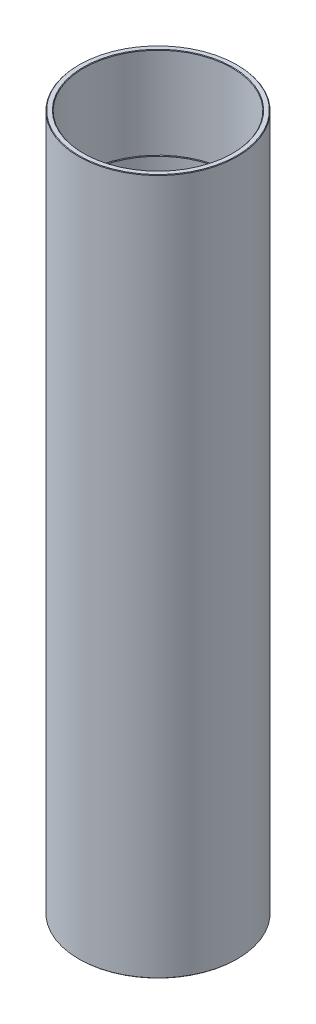
SolidWorks part; units mm, degrees
material "Технически чистый Сорт 2 продольный (SS)"
ref_plane "Спереди" through (0, 0, 0) normal (0, 0, 1) x (1, 0, 0)
ref_plane "Сверху" through (0, 0, 0) normal (0, 1, 0) x (1, 0, 0)
ref_plane "Справа" through (0, 0, 0) normal (1, 0, 0) x (0, 0, -1)
sketch "Эскиз1" plane through (0, 0, 0) normal (0, 0, 1) x (1, 0, 0)
  line L0 (0, 0) -> (0, 265) construction
  line L1 (-30.2, 0) -> (-30.2, 265)
  line L2 (-30.2, 265) -> (-28.25, 265)
  line L3 (-28.25, 265) -> (-28.25, 230)
  line L4 (-28.25, 230) -> (-28, 230)
  line L5 (-30.2, 0) -> (-28.25, 0)
  line L6 (-28.25, 0) -> (-28.25, 25)
  line L7 (-28.25, 25) -> (-28, 25)
  line L8 (-28, 25) -> (-28, 230)
  dimension "D1" = 30.2
  dimension "D2" = 28
  dimension "D3" = 28.25
  dimension "D4" = 28.25
  dimension "D5" = 25
  dimension "D6" = 35
revolve "Повернуть1" add sketch "Эскиз1" angle 360 about L0
chamfer "Фаска1" distance 0.2 angle 45 1 edges at (0, 265, -30.2)
chamfer "Фаска2" distance 0.2 angle 45 2 edges at (0, 230, -28.25) (0, 265, -28.25)
chamfer "Фаска3" distance 0.2 angle 45 1 edges at (0, 0, -30.2)
chamfer "Фаска4" distance 0.2 angle 45 1 edges at (0, 0, -28.25)
